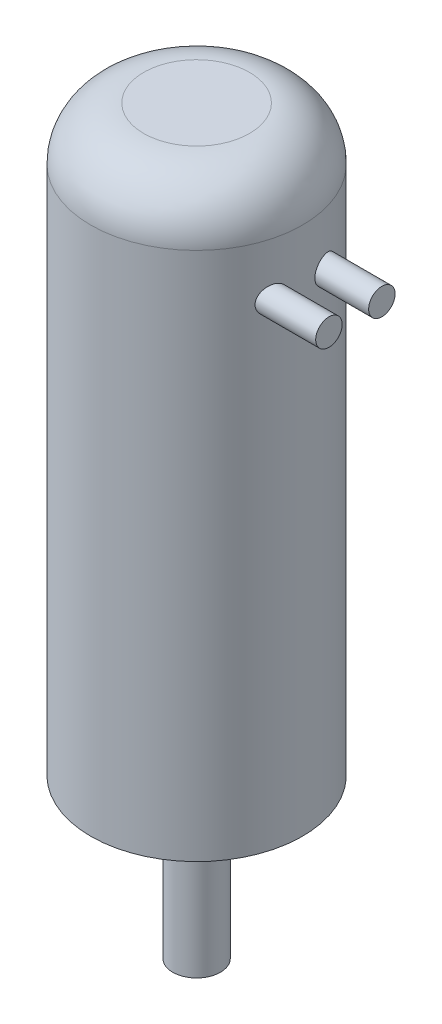
SolidWorks part; units mm, degrees
ref_plane "Front Plane" through (0, 0, 0) normal (0, 0, 1) x (1, 0, 0)
ref_plane "Top Plane" through (0, 0, 0) normal (0, 1, 0) x (1, 0, 0)
ref_plane "Right Plane" through (0, 0, 0) normal (1, 0, 0) x (0, 0, -1)
sketch "Sketch1" plane through (0, 0, 0) normal (0, 1, 0) x (1, 0, 0)
  circle A0 centre (0, 0) radius 20
extrude "Boss-Extrude1" add sketch "Sketch1" along normal blind 110
sketch "Sketch2" plane through (0, 0, 0) normal (0, 1, 0) x (1, 0, 0)
  circle A1 centre (15, 0) radius 3
  circle A2 centre (-15, 0) radius 3
extrude "Cut-Extrude1" cut sketch "Sketch2" along normal blind 25
cosmetic thread "Cosmetic Thread1" parameters "D1"=20, "D2"=8
cosmetic thread "Cosmetic Thread2" parameters "D1"=20, "D2"=8
sketch "Sketch3" plane through (0, 0, 0) normal (0, 1, 0) x (1, 0, 0)
  circle A0 centre (0, 0) radius 4.5
extrude "Boss-Extrude2" add sketch "Sketch3" against normal blind 30
fillet "Fillet1" radius 10 1 edges at (0, 110, 20)
ref_plane "Plane1" through (30, 0, 0) normal (1, 0, 0) x (0, 0, -1)
sketch "Sketch4" plane through (30, 0, 0) normal (1, 0, 0) x (0, 0, -1)
  circle A2 centre (5, 90) radius 2.5
  circle A3 centre (-5, 90) radius 2.5
extrude "Boss-Extrude3" add sketch "Sketch4" against normal up to surface (11.4595 mm away)
